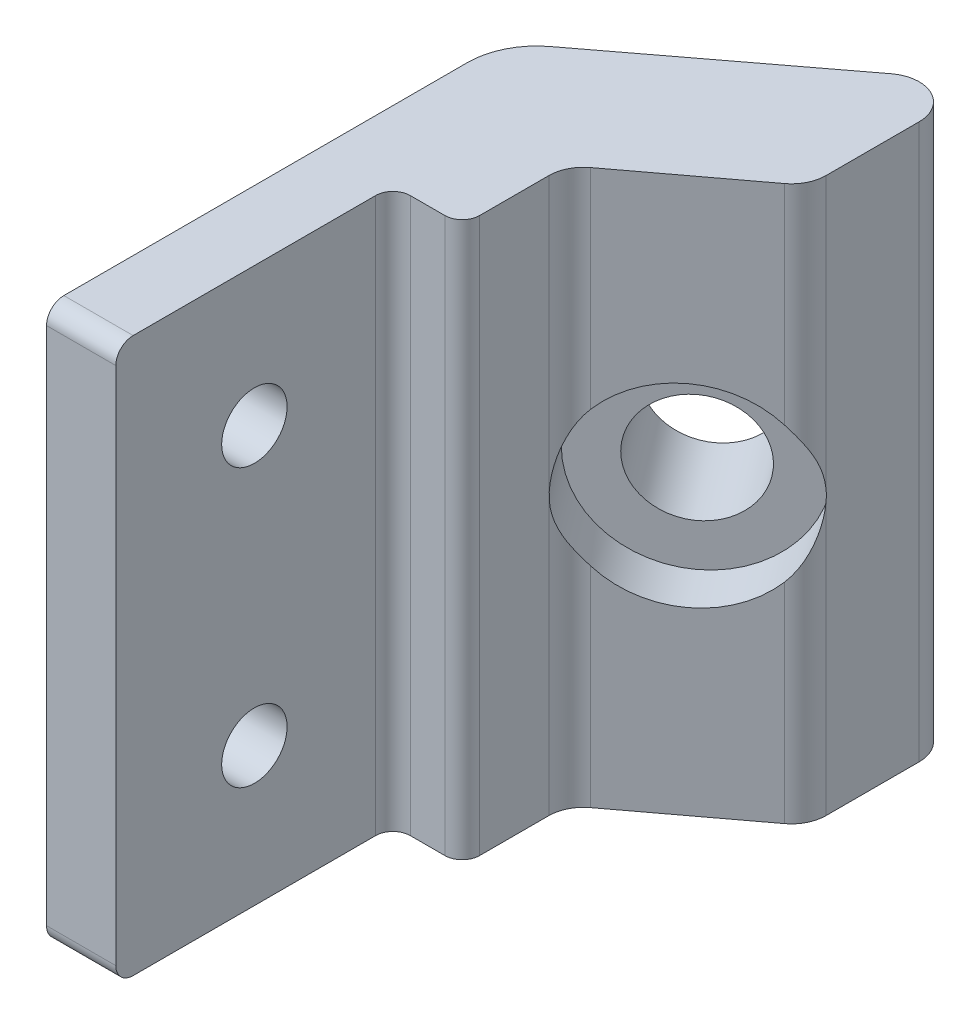
SolidWorks part; units mm, degrees
ref_plane "Front Plane" through (0, 0, 0) normal (0, 0, 1) x (1, 0, 0)
ref_plane "Top Plane" through (0, 0, 0) normal (0, 1, 0) x (1, 0, 0)
ref_plane "Right Plane" through (0, 0, 0) normal (1, 0, 0) x (0, 0, -1)
sketch "Sketch1" plane through (0, 0, 0) normal (0, 1, 0) x (1, 0, 0)
  line L31 (31.75, 0) -> (31.75, 13.1716)
  line L40 (31.75, 13.1716) -> (31.75, 38.5716)
  line L41 (34.2669, 43.6342) -> (52.0584, 57.105)
  line L42 (45.72, 35.8775) -> (55.88, 43.4975)
  line L43 (57.15, 46.0375) -> (57.15, 54.5737)
  line L45 (44.45, 26.9875) -> (44.45, 33.3375)
  line L46 (38.1, 0) -> (38.1, 23.8125)
  line L47 (39.6875, 25.4) -> (42.8625, 25.4)
  line L48 (31.75, 0) -> (38.1, 0)
  arc A18 (45.72, 35.8775) -> (44.45, 33.3375) centre (47.625, 33.3375) ccw
  arc A19 (55.88, 43.4975) -> (57.15, 46.0375) centre (53.975, 46.0375) ccw
  arc A20 (57.15, 54.5737) -> (52.0584, 57.105) centre (53.975, 54.5737) ccw
  arc A21 (34.2669, 43.6342) -> (31.75, 38.5716) centre (38.1, 38.5716) ccw
  arc A22 (44.45, 26.9875) -> (42.8625, 25.4) centre (42.8625, 26.9875) cw
  arc A23 (39.6875, 25.4) -> (38.1, 23.8125) centre (39.6875, 23.8125) ccw
  point P1 (57.15, -25.4)
  point P2 (44.45, 0)
  point P5 (38.1, 0)
  point P7 (57.15, 60.96)
  point P9 (57.15, 12.7)
  point P10 (57.15, 44.45)
  point P13 (44.45, 13.9971)
  point P14 (44.45, 13.9971)
  point P16 (31.75, 25.4)
  point P23 (38.1, -25.4)
  point P25 (31.75, 41.7286)
  point P31 (31.75, 16.3286)
  point P32 (31.75, -25.4)
  point P34 (44.45, 25.4)
  point P36 (38.1, 25.4)
  point P39 (31.75, 0)
  dimension "D1" = 3.175
  dimension "D3" = 6.35
  dimension "D2" = 1.5875
extrude "Boss-Extrude1" add sketch "Sketch1" against normal blind 50.8
sketch "Sketch15" plane through (-8.5131, 0, -11.2437) normal (-0.6036, 0, -0.7973) x (-0.7973, 0, 0.6036)
  circle A0 centre (-64.4923, -25.4) radius 5
  point P0 (-64.4923, -25.4)
extrude "Cut-Extrude14" cut sketch "Sketch15" against normal blind 8.89
ref_plane "Plane2" through (0.762, 0, 1.016) normal (0.6, 0, 0.8) x (0.8, 0, -0.6)
sketch "Sketch16" plane through (0.762, 0, 1.016) normal (0.6, 0, 0.8) x (0.8, 0, -0.6)
  circle A0 centre (64.4679, -25.4) radius 8.89
  point P0 (64.4679, -25.4)
extrude "Cut-Extrude15" cut sketch "Sketch16" against normal blind 6.858
sketch "Sketch17" plane through (31.75, 0, 0) normal (-1, 0, 0) x (0, 0, 1)
  line L0 (-1.5875, -50.8) -> (0, -50.8)
  line L1 (0, -50.8) -> (0, -49.2125)
  line L2 (-1.5875, 0) -> (0, 0)
  line L3 (0, 0) -> (0, -1.5875)
  circle A0 centre (-12.7, -12.7) radius 3
  circle A1 centre (-12.7, -38.1) radius 3
  arc A2 (0, -49.2125) -> (-1.5875, -50.8) centre (-1.5875, -49.2125) cw
  arc A3 (0, -1.5875) -> (-1.5875, 0) centre (-1.5875, -1.5875) ccw
  point P0 (-12.7, -12.7)
  point P1 (-12.7, -38.1)
  dimension "D1" = 1.5875
extrude "Cut-Extrude16" cut sketch "Sketch17" against normal blind 6.35
